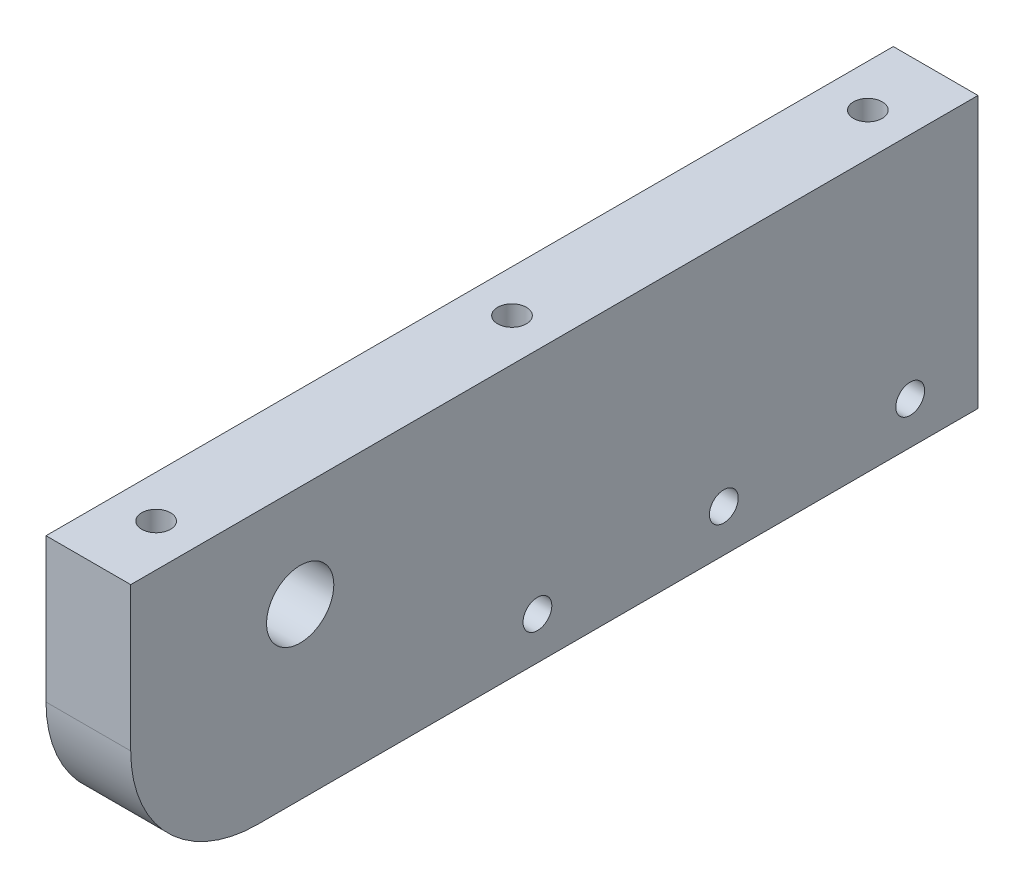
SolidWorks part; units mm, degrees
material "Plain Carbon Steel"
ref_plane "Front Plane" through (0, 0, 0) normal (0, 0, 1) x (1, 0, 0)
ref_plane "Top Plane" through (0, 0, 0) normal (0, 1, 0) x (1, 0, 0)
ref_plane "Right Plane" through (0, 0, 0) normal (1, 0, 0) x (0, 0, -1)
sketch "Sketch1" plane through (0, 0, 0) normal (1, 0, 0) x (0, 0, -1)
  line L1 (-50, -16) -> (50, -16)
  line L2 (-50, -16) -> (-50, 16)
  line L3 (-50, 16) -> (50, 16)
  line L4 (50, -16) -> (50, 16)
  line L5 (-50, -16) -> (50, 16) construction
  line L6 (-50, 16) -> (50, -16) construction
  circle A1 centre (-30, 4) radius 3.9688
  point P0 (0, 0)
  dimension "D3" = 7.9375
  dimension "D1" = 32
  dimension "D2" = 100
  dimension "D4" = 12
  dimension "D5" = 20
extrude "Boss-Extrude1" add sketch "Sketch1" along normal blind 10
fillet "Fillet1" radius 15 1 edges at (5, -16, 50)
hole_wizard "CBORE for M3 SHCS" positions "Sketch2" profile "Sketch3" counterbore size "M3" standard "ANSI Metric"
sketch "Sketch2" plane through (-616.2935, 26, -1323.2827) normal (0, 1, 0) x (1, 0, 0)
  line L3 (621.2935, -1281.2827) -> (621.2935, -1365.2827) construction
  line L5 (731.2935, -1281.2827) -> (731.2935, -1343.2827) construction
  circle A0 centre (731.2935, -1281.2827) radius 2.243
  circle A1 centre (731.2935, -1343.2827) radius 2.2384
  circle A3 centre (621.2935, -1281.2827) radius 2.3325
  circle A4 centre (621.2935, -1365.2827) radius 1.7576
  circle A5 centre (621.2935, -1323.2827) radius 1.8624
  circle A6 centre (731.2935, -1312.2827) radius 2.0271
  point P1 (731.2935, -1281.2827)
  point P8 (731.2935, -1343.2827)
  point P15 (621.2935, -1281.2827)
  point P17 (621.2935, -1365.2827)
  point P19 (621.2935, -1323.2827)
  point P27 (731.2935, -1312.2827)
sketch "Sketch3" plane through (115, 26, -42) normal (1, 0, 0) x (0, 0, 1)
  line L0 (0, 0) -> (0, 24.0215)
  line L1 (0, 24.0215) -> (1.7, 23)
  line L2 (1.7, 23) -> (1.7, 3)
  line L3 (1.7, 3) -> (3.25, 3)
  line L4 (3.25, 3) -> (3.25, 0)
  line L5 (3.25, 0) -> (0, 0)
  line L6 (0, 24.0215) -> (-1.7, 23) construction
  line L7 (0, -6.35) -> (0, 107.95) construction
  dimension "Hole Dia." = 3.4
  dimension "Hole Depth" = 23
  dimension "C'Bore Dia." = 6.5
  dimension "C'Bore Depth" = 3
  dimension "Drill Angle" = 118
hole_wizard "CBORE for M3 SHCS1" positions "Sketch4" profile "Sketch5" counterbore size "M3" standard "ANSI Metric"
sketch "Sketch4" plane through (0, -904.0121, -1323.2827) normal (-1, 0, 0) x (0, 0, 1)
  line L0 (1281.2827, 893.0121) -> (1325.2827, 893.0121) construction
  point P0 (1281.2827, 893.0121)
  point P1 (1325.2827, 893.0121)
  point P4 (1303.2827, 893.0121)
sketch "Sketch5" plane through (0, -11, -42) normal (0, 1, 0) x (0, 0, 1)
  line L0 (0, 0) -> (0, 24.0215)
  line L1 (0, 24.0215) -> (1.7, 23)
  line L2 (1.7, 23) -> (1.7, 3)
  line L3 (1.7, 3) -> (3.25, 3)
  line L4 (3.25, 3) -> (3.25, 0)
  line L5 (3.25, 0) -> (0, 0)
  line L6 (0, 24.0215) -> (-1.7, 23) construction
  line L7 (0, -6.35) -> (0, 107.95) construction
  dimension "Hole Dia." = 3.4
  dimension "Hole Depth" = 23
  dimension "C'Bore Dia." = 6.5
  dimension "C'Bore Depth" = 3
  dimension "Drill Angle" = 118
